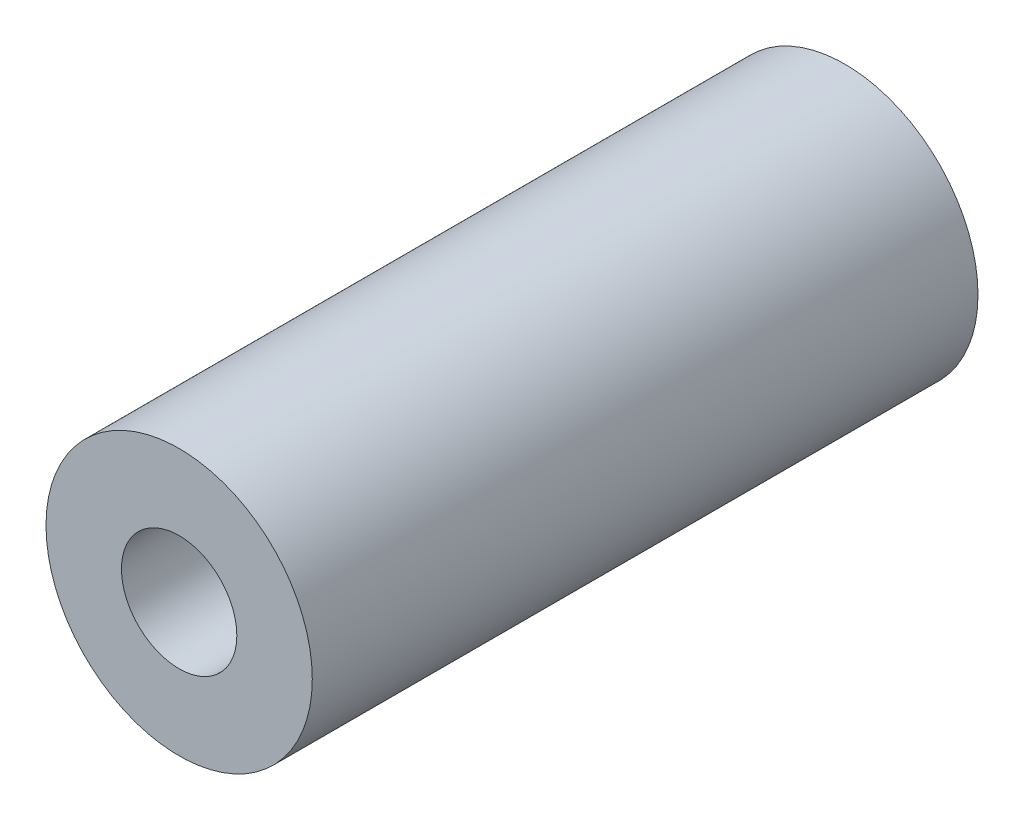
SolidWorks part; units mm, degrees
ref_plane "Front Plane" through (0, 0, 0) normal (0, 0, 1) x (1, 0, 0)
ref_plane "Top Plane" through (0, 0, 0) normal (0, 1, 0) x (1, 0, 0)
ref_plane "Right Plane" through (0, 0, 0) normal (1, 0, 0) x (0, 0, -1)
sketch "Sketch1" plane through (0, 0, 0) normal (0, 0, 1) x (1, 0, 0)
  circle A0 centre (0, 0) radius 2.6
  circle A1 centre (0, 0) radius 6
  dimension "D1" = 5.2
  dimension "D2" = 12
extrude "Boss-Extrude1" add sketch "Sketch1" along normal blind 30
